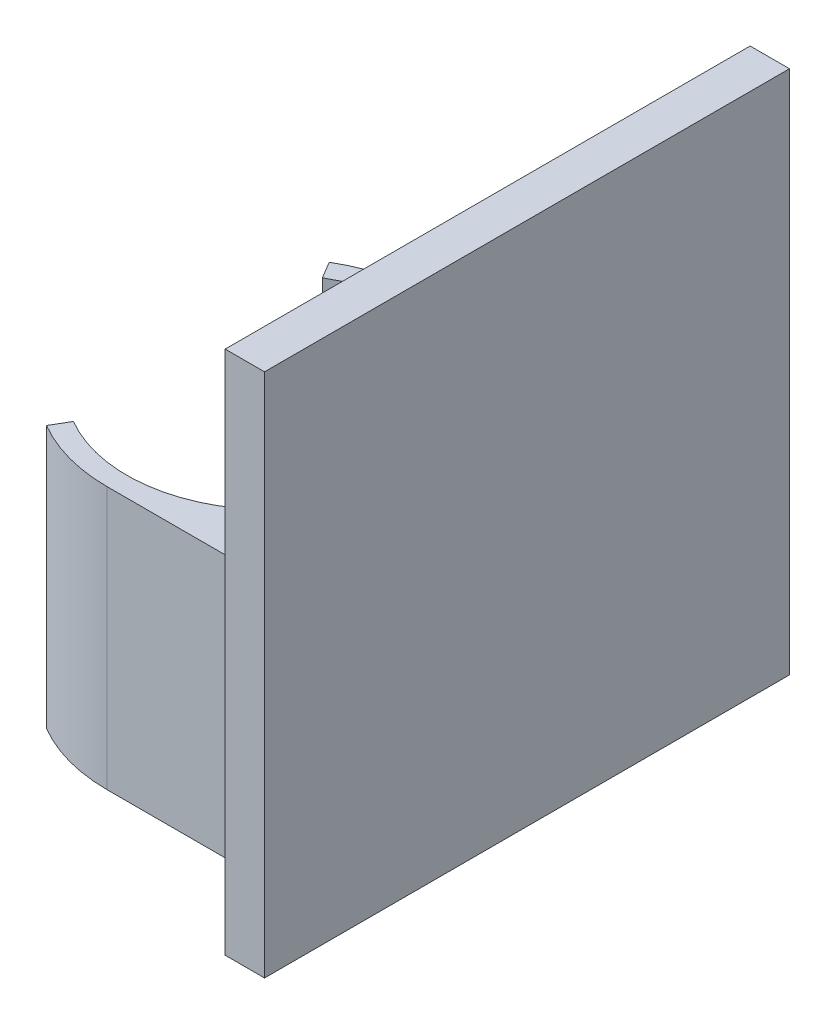
SolidWorks part; units mm, degrees
ref_plane "Front Plane" through (0, 0, 0) normal (0, 0, 1) x (1, 0, 0)
ref_plane "Top Plane" through (0, 0, 0) normal (0, 1, 0) x (1, 0, 0)
ref_plane "Right Plane" through (0, 0, 0) normal (1, 0, 0) x (0, 0, -1)
sketch "Sketch23" plane through (0, 0, 0) normal (0, 1, 0) x (1, 0, 0)
  line L1 (-12.5, -12.5) -> (12.5, -12.5)
  line L2 (-12.5, -12.5) -> (-12.5, 12.5)
  line L3 (-12.5, 12.5) -> (12.5, 12.5)
  line L4 (12.5, -12.5) -> (12.5, 12.5)
  line L5 (-12.5, -12.5) -> (12.5, 12.5) construction
  line L6 (-12.5, 12.5) -> (12.5, -12.5) construction
  point P0 (0, 0)
  dimension "D1" = 25
  dimension "D2" = 25
extrude "Boss-Extrude6" add sketch "Sketch23" along normal blind 20
sketch "Sketch24" plane through (0, 20, 0) normal (0, 1, 0) x (1, 0, 0)
  circle A0 centre (0, 0) radius 11
  dimension "D1" = 22
extrude "Cut-Extrude7" cut sketch "Sketch24" against normal through all
sketch "Sketch25" plane through (0, 20, 0) normal (0, 1, 0) x (1, 0, 0)
  line L0 (0, 12.5) -> (-12.5, 12.5)
  line L1 (-12.5, 12.5) -> (-12.5, -12.5)
  line L2 (-12.5, -12.5) -> (0, -12.5)
  line L3 (-6.3399, 10.7729) -> (-5.5791, 9.4802)
  line L4 (-6.3399, -10.7729) -> (-5.5791, -9.4802)
  arc A0 (0, 12.5) -> (-6.3399, 10.7729) centre (0, 0) ccw
  circle A1 centre (0, 0) radius 11 construction
  arc A2 (-5.5791, 9.4802) -> (-5.5791, -9.4802) centre (0, 0) ccw
  arc A3 (-6.3399, -10.7729) -> (0, -12.5) centre (0, 0) ccw
extrude "Cut-Extrude8" cut sketch "Sketch25" against normal through all
ref_plane "Plane6" through (16.5, 0, 0) normal (1, 0, 0) x (0, 0, -1)
sketch "Sketch26" plane through (16.5, 0, 0) normal (1, 0, 0) x (0, 0, -1)
  line L5 (-20, 1.0751) -> (20, 1.0751)
  line L6 (-20, 1.0751) -> (-20, 41.0751)
  line L7 (-20, 41.0751) -> (20, 41.0751)
  line L8 (20, 1.0751) -> (20, 41.0751)
  line L9 (-20, 1.0751) -> (20, 41.0751) construction
  line L10 (-20, 41.0751) -> (20, 1.0751) construction
  point P0 (0, 21.0751)
  point P6 (0, 0)
  dimension "D1" = 40
  dimension "D2" = 40
extrude "Boss-Extrude7" add sketch "Sketch26" along normal blind 3 separate body
